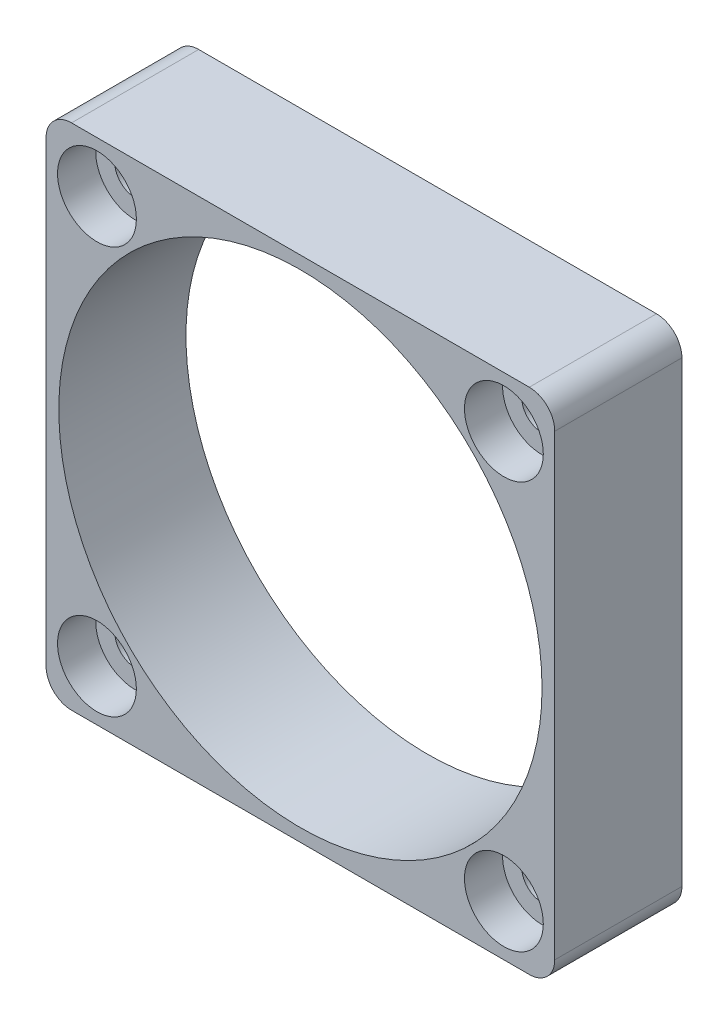
SolidWorks part; units mm, degrees
material "PUR"
ref_plane "Front Plane" through (0, 0, 0) normal (0, 0, 1) x (1, 0, 0)
ref_plane "Top Plane" through (0, 0, 0) normal (0, 1, 0) x (1, 0, 0)
ref_plane "Right Plane" through (0, 0, 0) normal (1, 0, 0) x (0, 0, -1)
sketch "Sketch1" plane through (0, 0, 0) normal (0, 0, 1) x (1, 0, 0)
  line L1 (-20, 20) -> (20, 20)
  line L2 (-20, 20) -> (-20, -20)
  line L3 (-20, -20) -> (20, -20)
  line L4 (20, 20) -> (20, -20)
  line L5 (-20, 20) -> (20, -20) construction
  line L6 (-20, -20) -> (20, 20) construction
  point P0 (0, 0)
  dimension "D1" = 40
extrude "Boss-Extrude1" add sketch "Sketch1" along normal blind 10
sketch "Sketch2" plane through (0, 0, 10) normal (0, 0, 1) x (1, 0, 0)
  line L1 (-16, -16) -> (16, -16) construction
  line L2 (-16, -16) -> (-16, 16) construction
  line L3 (-16, 16) -> (16, 16) construction
  line L4 (16, -16) -> (16, 16) construction
  line L5 (-16, -16) -> (16, 16) construction
  line L6 (-16, 16) -> (16, -16) construction
  circle A0 centre (0, 0) radius 19
  circle A1 centre (-16, 16) radius 1.6
  circle A2 centre (16, 16) radius 1.6
  circle A3 centre (16, -16) radius 1.6
  circle A4 centre (-16, -16) radius 1.6
  dimension "D1" = 38
  dimension "D3" = 3.2
  dimension "D2" = 32
extrude "Cut-Extrude1" cut sketch "Sketch2" against normal through all
fillet "Fillet1" radius 2 4 edges at (-20, -20, 5) (-20, 20, 5) (20, -20, 5) (20, 20, 5)
sketch "Sketch3" plane through (0, 0, 10) normal (0, 0, 1) x (1, 0, 0)
  circle A0 centre (-16, -16) radius 3.1
  circle A1 centre (16, -16) radius 3.1
  circle A2 centre (16, 16) radius 3.1
  circle A3 centre (-16, 16) radius 3.1
  dimension "D1" = 6.2
extrude "Cut-Extrude2" cut sketch "Sketch3" against normal blind 3
